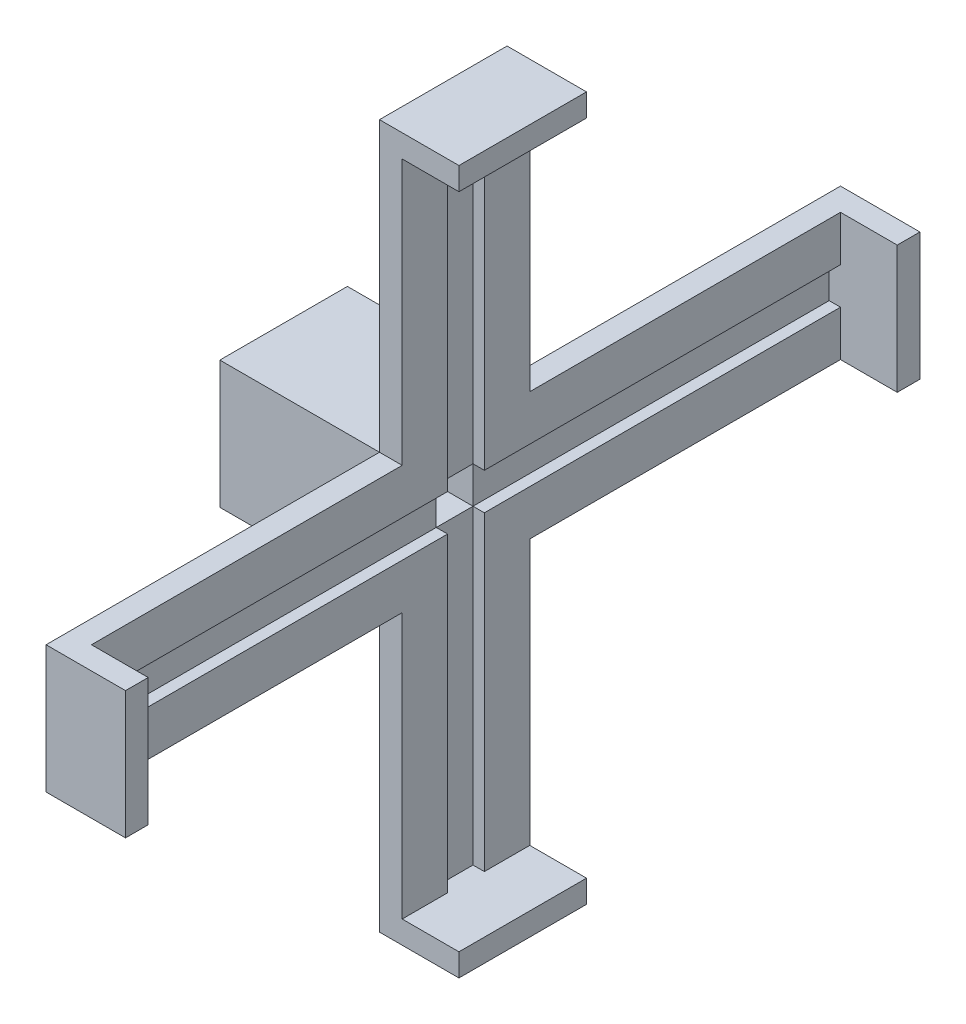
SolidWorks part; units mm, degrees
ref_plane "Front Plane" through (0, 0, 0) normal (0, 0, 1) x (1, 0, 0)
ref_plane "Top Plane" through (0, 0, 0) normal (0, 1, 0) x (1, 0, 0)
ref_plane "Right Plane" through (0, 0, 0) normal (1, 0, 0) x (0, 0, -1)
sketch "Sketch1" plane through (0, 0, 0) normal (0, 0, 1) x (1, 0, 0)
  circle A0 centre (0, 0) radius 28.1
extrude "Boss-Extrude2" add sketch "Sketch1" along normal blind 24
sketch "Sketch3" plane through (0, 0, 0) normal (0, 0, -1) x (-1, 0, 0)
  line L2 (-1.6618, 2.5) -> (1.6618, 2.5)
  arc A1 (-1.6618, 2.5) -> (1.6618, 2.5) centre (0, 0) ccw
  point P4 (1.6623, 2.4983)
extrude "Cut-Extrude2" cut sketch "Sketch3" against normal blind 21.5
sketch "Sketch4" plane through (0, 0, 0) normal (0, 0, -1) x (-1, 0, 0)
  circle A0 centre (0, 0) radius 3
extrude "Cut-Extrude3" cut sketch "Sketch4" against normal blind 9.5
sketch "Sketch6" plane through (0, 0, 0) normal (0, 0, -1) x (-1, 0, 0)
  circle A0 centre (0, 0) radius 6.025
extrude "Cut-Extrude4" cut sketch "Sketch6" against normal blind 6.2
sketch "Sketch7" plane through (0, 0, 24) normal (0, 0, 1) x (1, 0, 0)
  line L1 (-28.1, -28.1) -> (28.1, -28.1)
  line L2 (-28.1, -28.1) -> (-28.1, 28.1)
  line L3 (-28.1, 28.1) -> (28.1, 28.1)
  line L4 (28.1, -28.1) -> (28.1, 28.1)
  line L5 (-28.1, -28.1) -> (28.1, 28.1) construction
  line L6 (-28.1, 28.1) -> (28.1, -28.1) construction
  point P0 (0, 0)
extrude "Boss-Extrude3" add sketch "Sketch7" along normal blind 56.2
sketch "Sketch8" plane through (28.1, 0, 0) normal (1, 0, 0) x (0, 0, -1)
  line L0 (-80.2, 28.1) -> (-24, 28.1) construction
  line L1 (-80.2, 28.1) -> (-24, 28.1)
  line L2 (-80.2, 28.1) -> (-80.2, -28.1)
  line L3 (-80.2, -28.1) -> (-24, -28.1)
  line L4 (-24, 28.1) -> (-24, -28.1)
  line L5 (-80.2, -28.1) -> (-80.2, 28.1) construction
extrude "Boss-Extrude4" add sketch "Sketch8" along normal blind 14.14
sketch "Sketch10" plane through (42.24, 0, 0) normal (1, 0, 0) x (0, 0, -1)
  line L1 (-80.2, 28.1) -> (-24, 28.1)
  line L2 (-80.2, 28.1) -> (-80.2, -28.1)
  line L3 (-80.2, -28.1) -> (-24, -28.1)
  line L4 (-24, 28.1) -> (-24, -28.1)
extrude "Boss-Extrude5" add sketch "Sketch10" along normal blind 10
sketch "Sketch11" plane through (0, 0, 80.2) normal (0, 0, 1) x (1, 0, 0)
  line L1 (52.24, 28.1) -> (-28.1, 28.1) construction
  line L3 (42.24, 28.1) -> (52.24, 28.1)
  line L4 (42.24, 28.1) -> (42.24, -28.1)
  line L5 (42.24, -28.1) -> (52.24, -28.1)
  line L6 (52.24, 28.1) -> (52.24, -28.1)
extrude "Boss-Extrude6" add sketch "Sketch11" along normal blind 146.9
sketch "Sketch12" plane through (0, 28.1, 0) normal (0, 1, 0) x (1, 0, 0)
  line L1 (42.24, -80.2) -> (52.24, -80.2)
  line L2 (42.24, -80.2) -> (42.24, -24)
  line L3 (42.24, -24) -> (52.24, -24)
  line L4 (52.24, -80.2) -> (52.24, -24)
extrude "Boss-Extrude7" add sketch "Sketch12" along normal blind 126.9
sketch "Sketch13" plane through (0, 0, 24) normal (0, 0, -1) x (-1, 0, 0)
  line L1 (-52.24, -28.1) -> (-42.24, -28.1)
  line L2 (-52.24, -28.1) -> (-52.24, 28.1)
  line L3 (-52.24, 28.1) -> (-42.24, 28.1)
  line L4 (-42.24, -28.1) -> (-42.24, 28.1)
extrude "Boss-Extrude8" add sketch "Sketch13" along normal blind 146.9
sketch "Sketch14" plane through (0, -28.1, 0) normal (0, -1, 0) x (-1, 0, 0)
  line L0 (-52.24, -227.1) -> (-52.24, 122.9) construction
  line L1 (-42.24, -24) -> (-52.24, -24)
  line L2 (-42.24, -24) -> (-42.24, -80.2)
  line L3 (-42.24, -80.2) -> (-52.24, -80.2)
  line L4 (-52.24, -24) -> (-52.24, -80.2)
extrude "Boss-Extrude9" add sketch "Sketch14" along normal blind 126.9
sketch "Sketch15" plane through (52.24, 0, 0) normal (1, 0, 0) x (0, 0, -1)
  line L1 (-80.2, 28.1) -> (-227.1, 28.1) construction
  line L3 (-217.1, 28.1) -> (-227.1, 28.1)
  line L4 (-217.1, 28.1) -> (-217.1, -28.1)
  line L5 (-217.1, -28.1) -> (-227.1, -28.1)
  line L6 (-227.1, 28.1) -> (-227.1, -28.1)
  point P7 (-222.1, 28.1)
extrude "Boss-Extrude10" add sketch "Sketch15" along normal blind 25
sketch "Sketch16" plane through (52.24, 0, 0) normal (1, 0, 0) x (0, 0, -1)
  line L1 (122.9, 28.1) -> (-24, 28.1) construction
  line L3 (112.9, 28.1) -> (122.9, 28.1)
  line L4 (112.9, 28.1) -> (112.9, -28.1)
  line L5 (112.9, -28.1) -> (122.9, -28.1)
  line L6 (122.9, 28.1) -> (122.9, -28.1)
extrude "Boss-Extrude11" add sketch "Sketch16" along normal blind 25
sketch "Sketch17" plane through (52.24, 0, 0) normal (1, 0, 0) x (0, 0, -1)
  line L1 (-80.2, 155) -> (-80.2, 28.1) construction
  line L3 (-80.2, 145) -> (-24, 145)
  line L4 (-80.2, 145) -> (-80.2, 155)
  line L5 (-80.2, 155) -> (-24, 155)
  line L6 (-24, 145) -> (-24, 155)
extrude "Boss-Extrude12" add sketch "Sketch17" along normal blind 25
sketch "Sketch18" plane through (52.24, 0, 0) normal (1, 0, 0) x (0, 0, -1)
  line L1 (-80.2, -155) -> (-80.2, -28.1) construction
  line L3 (-80.2, -145) -> (-24, -145)
  line L4 (-80.2, -145) -> (-80.2, -155)
  line L5 (-80.2, -155) -> (-24, -155)
  line L6 (-24, -145) -> (-24, -155)
extrude "Boss-Extrude13" add sketch "Sketch18" along normal blind 25
sketch "Sketch19" plane through (-28.1, 0, 0) normal (-1, 0, 0) x (0, 0, 1)
  line L7 (26.5, 25.6) -> (77.7, 25.6)
  line L8 (26.5, 25.6) -> (26.5, -25.6)
  line L9 (26.5, -25.6) -> (77.7, -25.6)
  line L10 (77.7, 25.6) -> (77.7, -25.6)
extrude "Cut-Extrude5" cut sketch "Sketch19" against normal blind 63.7
sketch "Sketch20" plane through (0, 0, 0) normal (0, 0, -1) x (-1, 0, 0)
  arc A1 (0, 15) -> (-15, 0) centre (0, 0) ccw
sketch3d "3DSketch2"
  line L2 (0, 15, 0) -> (0, 22.5, 0)
  line L3 (0, 15, 0) -> (0, 15, 42.1431)
  line L4 (0, 15, 42.1431) -> (0, 22.5, 42.1431)
  line L5 (0, 22.5, 0) -> (0, 22.5, 42.1431)
  arc A0 (0, 15, 0) -> (15, 0, 0) centre (0, 0, 0) ccw construction
  point P10 (0, 0, -15)
sweep "Cut-Sweep2" cut profiles "3DSketch2" path "Sketch20"
sketch "Sketch23" plane through (52.24, 0, 0) normal (1, 0, 0) x (0, 0, -1)
  line L1 (-217.1, -28.1) -> (-217.1, 28.1) construction
  line L3 (112.9, 28.1) -> (112.9, -28.1) construction
  line L4 (-217.1, 8.1) -> (112.9, 8.1)
  line L5 (-217.1, 8.1) -> (-217.1, -8.1)
  line L6 (-217.1, -8.1) -> (112.9, -8.1)
  line L7 (112.9, 8.1) -> (112.9, -8.1)
extrude "Cut-Extrude7" cut sketch "Sketch23" against normal blind 5
sketch "Sketch24" plane through (52.24, 0, 0) normal (1, 0, 0) x (0, 0, -1)
  line L1 (-80.2, 145) -> (-24, 145) construction
  line L3 (-24, -145) -> (-80.2, -145) construction
  line L4 (-60.2, 145) -> (-44, 145)
  line L5 (-60.2, 145) -> (-60.2, -145)
  line L6 (-60.2, -145) -> (-44, -145)
  line L7 (-44, 145) -> (-44, -145)
extrude "Cut-Extrude8" cut sketch "Sketch24" against normal blind 5
sketch "Sketch25" plane through (47.24, 0, 0) normal (1, 0, 0) x (0, 0, -1)
  line L1 (-60.2, 8.1) -> (-44, 8.1)
  line L2 (-60.2, 8.1) -> (-60.2, -8.1)
  line L3 (-60.2, -8.1) -> (-44, -8.1)
  line L4 (-44, 8.1) -> (-44, -8.1)
extrude "Cut-Extrude12" cut sketch "Sketch25" against normal blind 25
